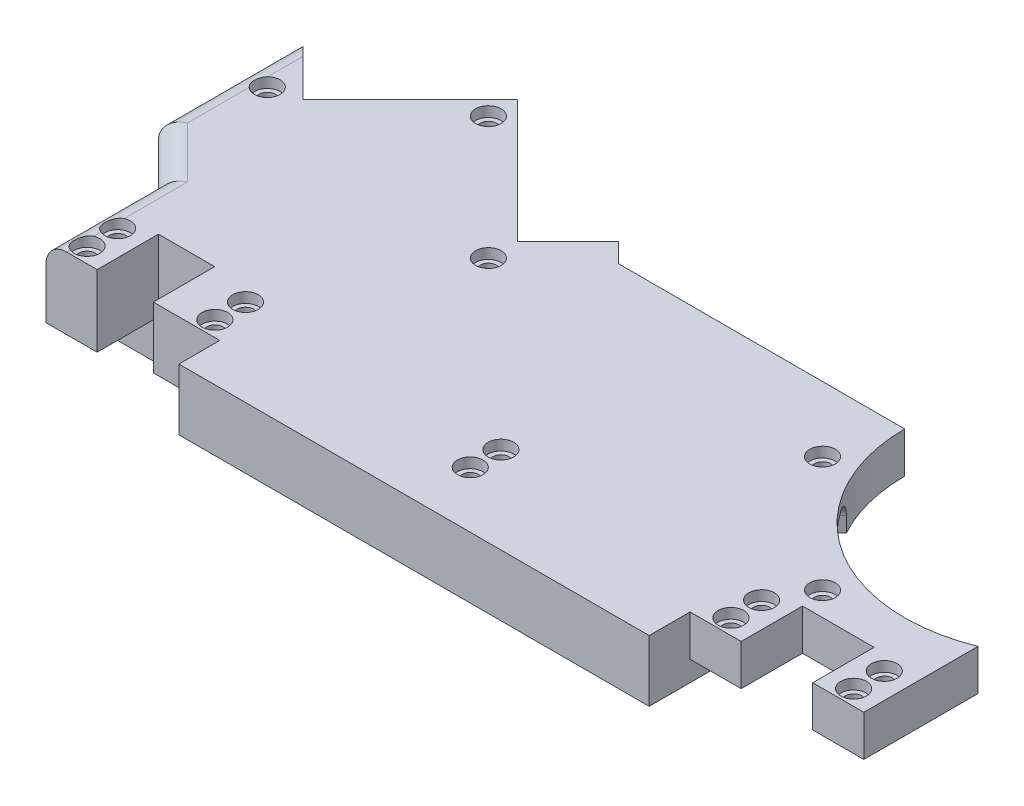
SolidWorks part; units mm, degrees
ref_plane "Front" through (0, 0, 0) normal (0, 0, 1) x (1, 0, 0)
ref_plane "Top" through (0, 0, 0) normal (0, 1, 0) x (1, 0, 0)
ref_plane "Right" through (0, 0, 0) normal (1, 0, 0) x (0, 0, -1)
sketch "Sketch1" plane through (0, 0, 0) normal (0, 1, 0) x (1, 0, 0)
  line L0 (24.9942, 10.5177) -> (0.9942, 10.5177)
  line L1 (0.9942, 10.5177) -> (-0.8991, 12.4111)
  line L2 (-0.8991, 12.4111) -> (-5.8489, 7.4613)
  line L3 (-5.8489, 7.4613) -> (-17.8698, 19.4823)
  line L4 (-17.8698, 19.4823) -> (-28.349, 9.0031)
  line L5 (-28.349, 9.0031) -> (-34.0058, 14.66)
  line L6 (-34.0058, 14.66) -> (-34.0058, 0.5177)
  line L7 (-34.0058, 0.5177) -> (-29.0058, -4.4823)
  line L8 (-29.0058, -4.4823) -> (-29.0058, -9.4823)
  line L9 (-29.0058, -9.4823) -> (-12.0058, -9.4823)
  line L10 (13.4942, -16.4823) -> (32.9942, -16.4823)
  line L11 (-19.9911, 15.9467) -> (-5.849, 1.8046)
  line L12 (-12.0058, -9.4823) -> (-12.0058, -19.4823)
  line L13 (-12.0058, -19.4823) -> (33.9942, -19.4823)
  line L14 (1.8642, 9.5177) -> (24.9942, 9.5177)
  line L15 (8.4942, -9.4823) -> (13.4942, -9.4823)
  line L16 (24.9942, 9.5177) -> (24.9942, -0.5929)
  line L17 (1.8642, 9.5177) -> (-5.849, 1.8046)
  line L18 (45.9942, -15.4823) -> (50.9942, -15.4823)
  line L21 (24.9942, 10.5177) -> (28.9942, 10.5177)
  line L23 (32.9942, -16.4823) -> (32.9942, -8.5929)
  line L24 (33.9942, -19.4823) -> (33.9942, -15.4823)
  line L25 (33.9942, -15.4823) -> (38.9942, -15.4823)
  line L26 (38.9942, -15.4823) -> (38.9942, -9.4823)
  line L27 (32.9942, -8.5929) -> (24.9942, -0.5929)
  line L28 (38.9942, -9.4823) -> (45.9942, -9.4823)
  line L29 (45.9942, -9.4823) -> (45.9942, -15.4823)
  line L36 (-19.9911, 15.9467) -> (-33.0058, 2.932)
  line L37 (-33.0058, 2.932) -> (-33.0058, 0.932)
  line L38 (-33.0058, 0.932) -> (-28.0058, -4.068)
  line L39 (-28.0058, -4.068) -> (-28.0058, -8.4823)
  line L40 (-28.0058, -8.4823) -> (-11.0058, -8.4823)
  line L42 (-11.0058, -8.4823) -> (-11.0058, -16.4823)
  line L43 (-11.0058, -16.4823) -> (8.4942, -16.4823)
  line L44 (8.4942, -16.4823) -> (8.4942, -9.4823)
  line L45 (13.4942, -9.4823) -> (13.4942, -16.4823)
  line L52 (50.9942, -15.4823) -> (50.9942, -4.3146)
  arc A3 (28.9942, 10.5177) -> (50.9942, -4.3146) centre (44.9942, 10.5177) ccw
extrude "Boss-Extrude1" add sketch "Sketch1" along normal blind 11
sketch "Sketch3" plane through (0, 0, 0) normal (0, 1, 0) x (1, 0, 0)
  line L0 (-17.8698, 19.4823) -> (-5.8489, 7.4613)
  line L1 (-5.8489, 7.4613) -> (-0.8991, 12.4111)
  line L2 (-0.8991, 12.4111) -> (0.9942, 10.5177)
  line L3 (0.9942, 10.5177) -> (24.9942, 10.5177)
  line L4 (33.9942, -19.4823) -> (33.9942, -15.4823)
  line L5 (24.9942, 10.5177) -> (28.9942, 10.5177)
  line L6 (50.9942, -4.3146) -> (50.9942, -15.4823)
  line L10 (33.9942, -19.4823) -> (-12.0058, -19.4823)
  line L11 (-12.0058, -19.4823) -> (-12.0058, -9.4823)
  line L14 (-12.0058, -9.4823) -> (-29.0058, -9.4823)
  line L15 (-29.0058, -9.4823) -> (-29.0058, -4.4823)
  line L16 (-29.0058, -4.4823) -> (-34.0058, 0.5177)
  line L17 (-34.0058, 0.5177) -> (-34.0058, 14.66)
  line L18 (-34.0058, 14.66) -> (-28.349, 9.0031)
  line L19 (-28.349, 9.0031) -> (-17.8698, 19.4823)
  line L28 (33.9942, -15.4823) -> (38.9942, -15.4823)
  line L29 (38.9942, -15.4823) -> (38.9942, -9.4823)
  line L30 (38.9942, -9.4823) -> (45.9942, -9.4823)
  line L31 (45.9942, -9.4823) -> (45.9942, -15.4823)
  line L32 (45.9942, -15.4823) -> (50.9942, -15.4823)
  arc A0 (28.9942, 10.5177) -> (50.9942, -4.3146) centre (44.9942, 10.5177) ccw
extrude "Boss-Extrude2" add sketch "Sketch3" against normal blind 1 from offset 11
sketch "Sketch5" plane through (0, 0, 0) normal (0, 1, 0) x (1, 0, 0)
  line L0 (-29.0058, -9.4823) -> (-29.0058, -15.4823)
  line L1 (-29.0058, -15.4823) -> (-24.0058, -15.4823)
  line L2 (-24.0058, -15.4823) -> (-24.0058, -9.4823)
  line L4 (-24.0058, -9.4823) -> (-29.0058, -9.4823)
  line L5 (-12.0058, -9.4823) -> (-18.5058, -9.4823)
  line L6 (-18.5058, -9.4823) -> (-18.5058, -15.4823)
  line L7 (-18.5058, -15.4823) -> (-12.0058, -15.4823)
  line L9 (-12.0058, -15.4823) -> (-12.0058, -9.4823)
extrude "Boss-Extrude3" add sketch "Sketch5" against normal blind 7 from offset 11
sketch "Sketch9" plane through (0.8062, 0, -0.8062) normal (0.7071, 0, -0.7071) x (-0.7071, 0, -0.7071)
  circle A0 centre (20.9119, 0) radius 2.25
extrude "Boss-Extrude4" add sketch "Sketch9" along normal blind 3
sketch "Sketch11" plane through (0, 0, 0) normal (0, 1, 0) x (1, 0, 0)
  line L0 (-17.8698, 19.4823) -> (-20.6982, 16.6538)
  line L2 (-20.6982, 16.6538) -> (-5.849, 1.8046)
  line L3 (-17.8698, 19.4823) -> (-5.8489, 7.4613)
  line L4 (-5.8489, 7.4613) -> (-0.8991, 12.4111)
  line L5 (-0.8991, 12.4111) -> (1.9292, 9.5828)
  line L6 (1.9292, 9.5828) -> (-5.849, 1.8046)
extrude "Boss-Extrude5" add sketch "Sketch11" against normal blind 5
sketch "Sketch7" plane through (-6.6551, 0, -6.6551) normal (-0.7071, 0, -0.7071) x (-0.7071, 0, 0.7071)
  line L0 (-4.6402, 0) -> (-4.6402, 11) construction
  line L2 (-4.6402, -6) -> (-4.6402, 0) construction
  line L4 (-4.6402, 0) -> (-4.6402, -2) construction
  line L5 (-4.6402, 0) -> (-4.6402, 2) construction
  circle A0 centre (-4.6402, 2) radius 1.75
  circle A1 centre (-4.6402, -2) radius 1.75
extrude "Tube Holes" cut sketch "Sketch7" against normal blind 4
sketch "Sketch8" plane through (0, 0, 0) normal (0, 1, 0) x (1, 0, 0)
  line L0 (24.9942, 10.5177) -> (0.9942, 10.5177)
  line L2 (-28.349, 9.0031) -> (-20.6982, 16.6538)
  line L4 (0.9942, 10.5177) -> (1.9292, 9.5828)
  line L5 (1.9292, 9.5828) -> (1.8642, 9.5177)
  line L6 (1.8642, 9.5177) -> (27.8642, -16.4823)
  line L7 (-20.6982, 16.6538) -> (-19.9911, 15.9467)
  line L10 (27.8642, -16.4823) -> (32.9942, -16.4823)
  line L11 (32.9942, -16.4823) -> (32.9942, -10.3696)
  line L13 (32.9942, -10.3696) -> (28.9317, -14.432)
  line L15 (-19.9911, 15.9467) -> (-27.6418, 8.296)
  line L17 (-27.6418, 8.296) -> (-28.349, 9.0031)
  line L18 (28.9317, -14.432) -> (20.0444, -5.5447)
  line L19 (20.0444, -5.5447) -> (24.9942, -0.595)
  line L20 (24.9942, -0.595) -> (24.9942, 10.5177)
extrude "Palm Tube Opening" cut sketch "Sketch8" along normal blind 10
sketch "Sketch12" plane through (0, 0, 0) normal (0, 1, 0) x (1, 0, 0)
  line L0 (33.9942, -19.4823) -> (33.9942, -9.5929)
  line L1 (-12.0058, -19.4823) -> (33.9942, -19.4823)
  line L2 (-12.0058, -19.4823) -> (-12.0058, -8.4823)
  line L3 (33.9942, -9.5929) -> (32.8835, -8.4823)
  line L6 (32.8835, -8.4823) -> (-12.0058, -8.4823)
extrude "Wrist Tube Opening" cut sketch "Sketch12" along normal blind 5
sketch "Sketch13" plane through (0, 0, 0) normal (0, 1, 0) x (1, 0, 0)
  line L1 (-29.0058, -15.4823) -> (-24.0058, -15.4823)
  line L2 (-29.0058, -15.4823) -> (-29.0058, -9.4823)
  line L3 (-29.0058, -9.4823) -> (-24.0058, -9.4823)
  line L4 (-24.0058, -15.4823) -> (-24.0058, -9.4823)
  line L5 (-18.5058, -15.4823) -> (-12.0058, -15.4823)
  line L6 (-18.5058, -15.4823) -> (-18.5058, -8.4823)
  line L7 (-18.5058, -8.4823) -> (-12.0058, -8.4823)
  line L8 (-12.0058, -15.4823) -> (-12.0058, -8.4823)
extrude "Cut-Extrude1" cut sketch "Sketch13" along normal blind 4
fillet "Fillet1" radius 2 3 edges at (-29.0058, 11, 9.9823) (-31.5058, 11, 1.9823) (-34.0058, 11, -7.5889)
sketch "Sketch14" plane through (-18.5058, 0, 0) normal (-1, 0, 0) x (0, 0, 1)
  line L2 (24.9766, -0.5) -> (19.4766, -0.5) construction
  line L3 (19.4766, -0.5) -> (8.4766, -0.5) construction
  line L4 (19.4766, -0.5) -> (19.4766, -6) construction
  line L5 (19.4766, -0.5) -> (19.4766, 5) construction
  line L6 (24.9766, 1) -> (23.4766, 1) construction
  line L7 (23.4766, 1) -> (23.4766, 4) construction
  line L8 (24.9766, 1) -> (23.4766, 4)
  line L9 (23.4766, 4) -> (23.4766, 5)
  line L10 (23.4766, 5) -> (19.4766, 5)
  line L11 (19.4766, 5) -> (14.2266, 5)
  line L12 (14.2266, 5) -> (14.2266, 4)
  line L13 (14.2266, 4) -> (8.4766, 4)
  line L14 (8.4766, 4) -> (8.4766, -0.5)
  line L15 (24.9766, -2) -> (23.4766, -2) construction
  line L16 (23.4766, -2) -> (23.4766, -5) construction
  line L17 (24.9766, -2) -> (23.4766, -5)
  line L18 (23.4766, -5) -> (23.4766, -6)
  line L19 (23.4766, -6) -> (19.4766, -6)
  line L20 (19.4766, -6) -> (14.2266, -6)
  line L21 (14.2266, -6) -> (14.2266, -5)
  line L22 (14.2266, -5) -> (8.4766, -5)
  line L23 (8.4766, -5) -> (8.4766, -0.5)
  line L24 (19.4766, -5.5) -> (19.4766, -0.5) construction
  line L25 (24.9766, -2) -> (24.9766, -0.5)
  line L26 (24.9766, -0.5) -> (24.9766, 1)
  line L27 (19.4766, 4.5) -> (19.4766, -0.5) construction
extrude "Pot Insert" cut sketch "Sketch14" against normal blind 2.5
sketch "Sketch6" plane through (0, 0, 0) normal (0, 1, 0) x (1, 0, 0)
  line L0 (-26.5001, -13.9766) -> (-26.5001, -15.4766) construction
  line L1 (44.9942, 10.5177) -> (33.6805, -0.796) construction
  line L2 (-26.5001, -13.9766) -> (-26.5001, -10.9766) construction
  line L3 (-14.0001, -13.9766) -> (-14.0001, -15.4766) construction
  line L4 (33.6805, -0.796) -> (32.9734, -1.5031) construction
  line L5 (-14.0001, -13.9766) -> (-14.0001, -10.9766) construction
  line L6 (-28.349, 9.0031) -> (-27.6418, 8.296) construction
  line L7 (-27.6418, 8.296) -> (-31.1418, 8.296) construction
  line L8 (10.9942, -19.4823) -> (10.9942, -13.9823) construction
  line L9 (32.9734, -1.5031) -> (27.3165, 4.1538) construction
  line L10 (32.9734, -1.5031) -> (38.6302, -7.1599) construction
  line L11 (10.9942, -13.9823) -> (10.9942, -10.9823) construction
  line L12 (-17.8698, 19.4823) -> (-16.4556, 18.068) construction
  line L13 (48.4942, -15.4823) -> (48.4942, -13.9823) construction
  line L14 (-16.4556, 18.068) -> (-17.8698, 16.6538) construction
  line L16 (48.4942, -13.9823) -> (48.4942, -10.9823) construction
  line L18 (-5.849, 7.4614) -> (-4.4348, 6.0472) construction
  line L19 (-4.4348, 6.0472) -> (-5.849, 4.633) construction
  line L21 (36.4942, -15.4823) -> (36.4942, -13.9823) construction
  line L22 (36.4942, -13.9823) -> (36.4942, -10.9823) construction
  circle A0 centre (-31.1418, 8.296) radius 0.8
  circle A1 centre (-26.5001, -10.9766) radius 0.8
  circle A2 centre (-26.5001, -13.9766) radius 0.8
  circle A3 centre (-14.0001, -13.9766) radius 0.8
  circle A4 centre (-14.0001, -10.9766) radius 0.8
  circle A5 centre (10.9942, -10.9823) radius 0.8
  circle A6 centre (10.9942, -13.9823) radius 0.8
  circle A7 centre (-17.8698, 16.6538) radius 0.8
  circle A8 centre (-5.849, 4.633) radius 0.8
  circle A10 centre (27.3165, 4.1538) radius 0.8
  circle A11 centre (38.6302, -7.1599) radius 0.8
  circle A12 centre (36.4942, -13.9823) radius 0.8
  circle A13 centre (36.4942, -10.9823) radius 0.8
  circle A14 centre (48.4942, -10.9823) radius 0.8
  circle A15 centre (48.4942, -13.9823) radius 0.8
extrude "Screw Holes" cut sketch "Sketch6" against normal through all from offset 12
sketch "Sketch10" plane through (0, 0, 0) normal (0, 1, 0) x (1, 0, 0)
  circle A0 centre (-17.8698, 16.6538) radius 1.25
  circle A1 centre (-31.1418, 8.296) radius 1.25
  circle A2 centre (-26.5001, -10.9766) radius 1.25
  circle A3 centre (-26.5001, -13.9766) radius 1.25
  circle A4 centre (-14.0001, -13.9766) radius 1.25
  circle A5 centre (-14.0001, -10.9766) radius 1.25
  circle A6 centre (10.9942, -10.9823) radius 1.25
  circle A7 centre (10.9942, -13.9823) radius 1.25
  circle A8 centre (-5.849, 4.633) radius 1.25
  circle A9 centre (27.3165, 4.1538) radius 1.25
  circle A10 centre (38.6302, -7.1599) radius 1.25
  circle A11 centre (36.4942, -10.9823) radius 1.25
  circle A12 centre (36.4942, -13.9823) radius 1.25
  circle A13 centre (48.4942, -10.9823) radius 1.25
  circle A14 centre (48.4942, -13.9823) radius 1.25
extrude "Screw Heads" cut sketch "Sketch10" against normal blind 2 from offset 12
sketch "Sketch15" plane through (0, 0, 0) normal (0, 1, 0) x (1, 0, 0)
  line L0 (24.9942, -0.5929) -> (24.9942, 10.5177)
  line L1 (24.9942, 10.5177) -> (28.9942, 10.5177)
  line L2 (24.9942, -0.5929) -> (33.9942, -9.5929)
  line L3 (33.9942, -15.4823) -> (38.9942, -15.4823)
  line L4 (38.9942, -15.4823) -> (38.9942, -9.4823)
  line L5 (33.9942, -9.5929) -> (33.9942, -15.4823)
  line L6 (38.9942, -9.4823) -> (45.9942, -9.4823)
  line L7 (45.9942, -9.4823) -> (45.9942, -15.4823)
  line L8 (45.9942, -15.4823) -> (50.9942, -15.4823)
  line L9 (50.9942, -15.4823) -> (50.9942, -4.3146)
  arc A0 (28.9942, 10.5177) -> (50.9942, -4.3146) centre (44.9942, 10.5177) ccw
extrude "Cut-Extrude2" cut sketch "Sketch15" along normal blind 7
sketch "Sketch19" plane through (12.2006, 0, -12.2006) normal (-0.7071, 0, 0.7071) x (0.7071, 0, 0.7071)
  line L0 (19.8785, 8.5) -> (19.8785, 7)
  line L1 (19.8785, 7) -> (28.8785, 7)
  line L4 (28.8785, 7) -> (28.8785, 8.5)
  line L5 (19.8785, 8.5) -> (21.3785, 8.5) construction
  line L6 (28.8785, 8.5) -> (27.3785, 8.5) construction
  line L7 (21.3785, 10) -> (27.3785, 10)
  arc A0 (19.8785, 8.5) -> (21.3785, 10) centre (21.3785, 8.5) cw
  arc A1 (28.8785, 8.5) -> (27.3785, 10) centre (27.3785, 8.5) ccw
extrude "Cut-Extrude4" cut sketch "Sketch19" against normal blind 7
